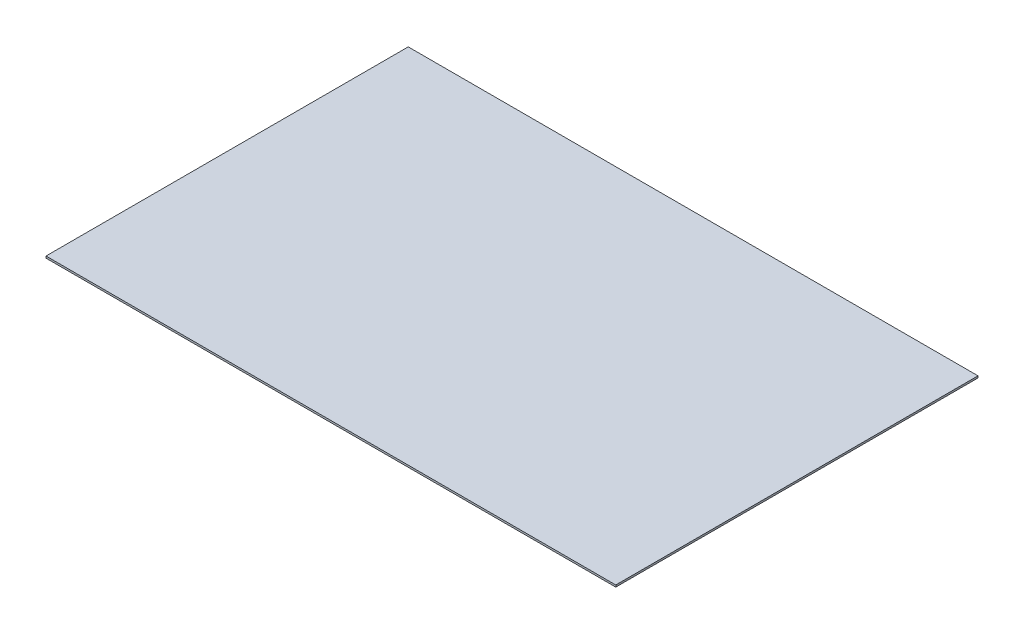
SolidWorks part; units mm, degrees
material "PC High Viscosity"
ref_plane "Front Plane" through (0, 0, 0) normal (0, 0, 1) x (1, 0, 0)
ref_plane "Top Plane" through (0, 0, 0) normal (0, 1, 0) x (1, 0, 0)
ref_plane "Right Plane" through (0, 0, 0) normal (1, 0, 0) x (0, 0, -1)
sketch "Sketch1" plane through (0, 0, 0) normal (0, 1, 0) x (1, 0, 0)
  line L1 (-239.7125, 152.4) -> (239.7125, 152.4)
  line L2 (-239.7125, 152.4) -> (-239.7125, -152.4)
  line L3 (-239.7125, -152.4) -> (239.7125, -152.4)
  line L4 (239.7125, 152.4) -> (239.7125, -152.4)
  line L5 (-239.7125, 152.4) -> (239.7125, -152.4) construction
  line L6 (-239.7125, -152.4) -> (239.7125, 152.4) construction
  point P0 (0, 0)
  dimension "D1" = 479.425
  dimension "D2" = 304.8
extrude "Boss-Extrude1" add sketch "Sketch1" along normal blind 1.5875
